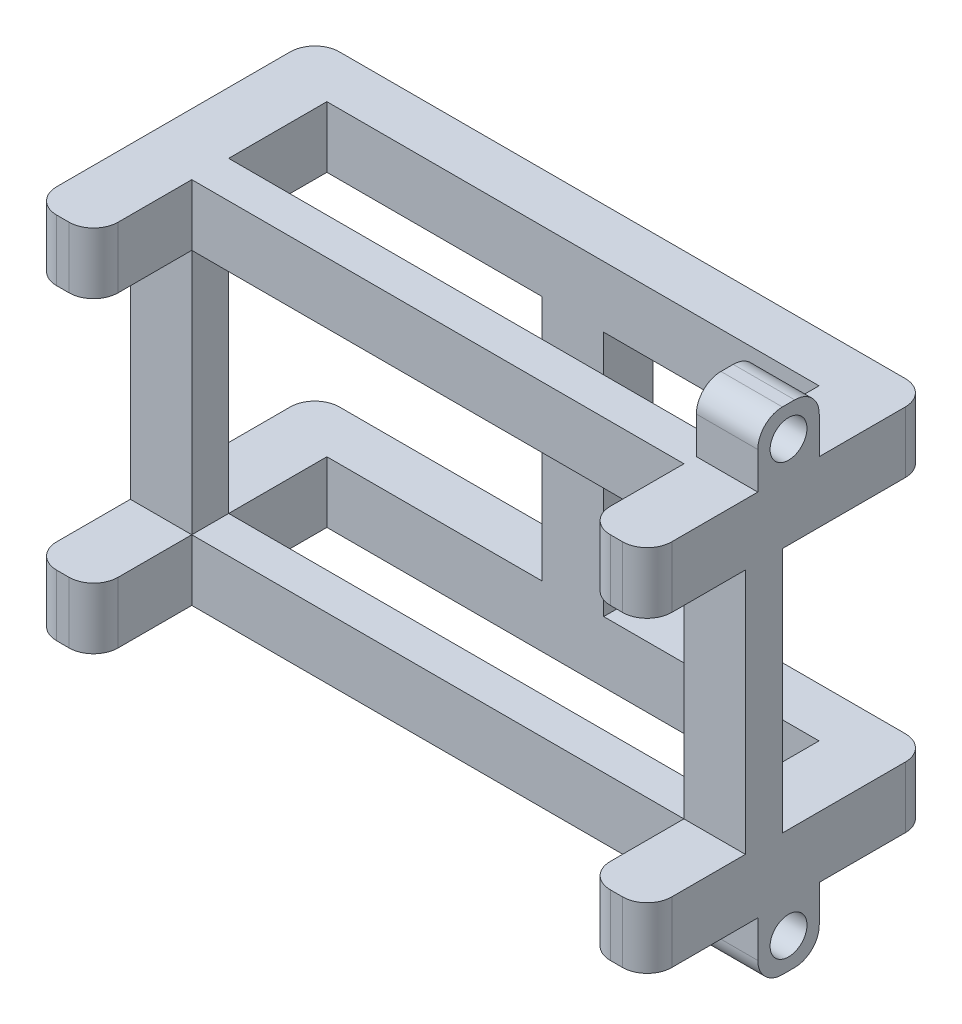
SolidWorks part; units mm, degrees
ref_plane "Front Plane" through (0, 0, 0) normal (0, 0, 1) x (1, 0, 0)
ref_plane "Top Plane" through (0, 0, 0) normal (0, 1, 0) x (1, 0, 0)
ref_plane "Right Plane" through (0, 0, 0) normal (1, 0, 0) x (0, 0, -1)
sketch "Sketch1" plane through (0, 0, 0) normal (0, 0, 1) x (1, 0, 0)
  line L0 (20.02, 5) -> (20.02, -25.04) construction
  line L1 (0, 0) -> (40.04, 0)
  line L2 (0, 0) -> (0, -20.04)
  line L3 (0, -20.04) -> (40.04, -20.04)
  line L4 (40.04, 0) -> (40.04, -20.04)
  line L5 (-5, 5) -> (45.04, 5)
  line L6 (-5, 5) -> (-5, -25.04)
  line L7 (-5, -25.04) -> (45.04, -25.04)
  line L8 (45.04, 5) -> (45.04, -25.04)
  line L10 (17.52, 0) -> (22.52, 0)
  line L11 (17.52, 0) -> (17.52, -20.04)
  line L12 (17.52, -20.04) -> (22.52, -20.04)
  line L13 (22.52, 0) -> (22.52, -20.04)
  line L14 (17.52, 0) -> (22.52, -20.04) construction
  line L15 (17.52, -20.04) -> (22.52, 0) construction
  point P11 (20.02, -10.02)
  dimension "D1" = 40.04
  dimension "D2" = 20.04
  dimension "D3" = 5
  dimension "D4" = 5
  dimension "D5" = 5
  dimension "D6" = 5
  dimension "D7" = 30.04
  dimension "D8" = 5
extrude "Boss-Extrude2" add sketch "Sketch1" along normal blind 28 contours L8 L5 L6 L7 L1 L4 L3 L2 | L13 L12 L11 L10
sketch "Sketch2" plane through (0, 0, 0) normal (0, 0, -1) x (-1, 0, 0)
  line L1 (-45.04, 5) -> (5, 5)
  line L2 (-45.04, 5) -> (-45.04, -25.04)
  line L3 (-45.04, -25.04) -> (5, -25.04)
  line L4 (5, 5) -> (5, -25.04)
  line L5 (-22.52, 0) -> (-40.04, 0)
  line L6 (-22.52, 0) -> (-22.52, -20.04)
  line L7 (-22.52, -20.04) -> (-40.04, -20.04)
  line L8 (-40.04, 0) -> (-40.04, -20.04)
  line L9 (-17.52, 0) -> (0, 0)
  line L10 (-17.52, 0) -> (-17.52, -20.04)
  line L11 (-17.52, -20.04) -> (0, -20.04)
  line L12 (0, 0) -> (0, -20.04)
extrude "Boss-Extrude3" add sketch "Sketch2" along normal blind 5
sketch "Sketch3" plane through (0, 0, 28) normal (0, 0, 1) x (1, 0, 0)
  line L6 (17.52, 0) -> (22.52, 0)
  line L7 (17.52, 0) -> (17.52, -20.04)
  line L8 (17.52, -20.04) -> (22.52, -20.04)
  line L9 (22.52, 0) -> (22.52, -20.04)
extrude "Cut-Extrude1" cut sketch "Sketch3" against normal blind 27
sketch "Sketch4" plane through (0, 0, -5) normal (0, 0, -1) x (-1, 0, 0)
  line L0 (-40.04, -20.04) -> (-45.04, -20.04) construction
  line L1 (-45.04, 5) -> (-45.04, -25.04) construction
  line L2 (-45.04, -20.04) -> (5, -20.04) construction
  line L3 (5, -25.04) -> (5, 5) construction
  line L4 (5, -20.04) -> (0, 0) construction
  line L5 (0, 0) -> (-45.04, 0) construction
  line L6 (-45.04, 0) -> (5, 0) construction
  line L8 (-45.04, 0) -> (-40.04, 0)
  line L9 (-45.04, 0) -> (-45.04, -20.04)
  line L10 (-45.04, -20.04) -> (-40.04, -20.04)
  line L11 (-40.04, 0) -> (-40.04, -20.04)
  line L12 (0, 0) -> (5, 0)
  line L13 (0, 0) -> (0, -20.04)
  line L14 (0, -20.04) -> (5, -20.04)
  line L15 (5, 0) -> (5, -20.04)
extrude "Cut-Extrude3" cut sketch "Sketch4" against normal blind 27
sketch "Sketch5" plane through (0, 5, 0) normal (0, 1, 0) x (1, 0, 0)
  line L0 (-5, -28) -> (45.04, -28) construction
  line L1 (0, -28) -> (40.04, -28)
  line L2 (0, -28) -> (0, 0.9809)
  line L3 (0, 0.9809) -> (40.04, 0.9809)
  line L4 (40.04, -28) -> (40.04, 0.9809)
  line L5 (-5, -28) -> (-5, 5) construction
  dimension "D1" = 5
  dimension "D2" = 40.04
extrude "Cut-Extrude4" cut sketch "Sketch5" against normal blind 47
sketch "Sketch6" plane through (0, 0, 0) normal (1, 0, 0) x (0, 0, -1)
  line L0 (5, -20.04) -> (-28, -20.04) construction
  line L1 (-28, 5) -> (-28, -25.04) construction
  line L2 (-28, -20.04) -> (-28, 0) construction
  line L3 (-28, 0) -> (5, 0) construction
  line L4 (-11.5, 0) -> (-11.5, -25.04) construction
  line L5 (-28, -25.04) -> (5, -25.04) construction
  line L6 (-11.5, -25.04) -> (-11.5, -20.04) construction
  line L7 (-11.5, -20.04) -> (-11.5, 0) construction
  line L8 (-11.5, 0) -> (-11.5, 5) construction
  line L9 (-28, 5) -> (5, 5) construction
  line L10 (-11.5, -20.04) -> (-11.5, -25.04) construction
  line L11 (-14, 5) -> (-9, 5)
  line L12 (-14, 5) -> (-14, 0)
  line L13 (-14, 0) -> (-9, 0)
  line L14 (-9, 5) -> (-9, 0)
  line L15 (-14, 5) -> (-9, 0) construction
  line L16 (-14, 0) -> (-9, 5) construction
  line L18 (-14, -20.04) -> (-9, -20.04)
  line L19 (-14, -20.04) -> (-14, -25.04)
  line L20 (-14, -25.04) -> (-9, -25.04)
  line L21 (-9, -20.04) -> (-9, -25.04)
  line L22 (-14, -20.04) -> (-9, -25.04) construction
  line L23 (-14, -25.04) -> (-9, -20.04) construction
  point P12 (-11.5, 2.5)
  point P21 (-11.5, -22.54)
  dimension "D1" = 5
  dimension "D2" = 5
extrude "Boss-Extrude4" add sketch "Sketch6" along normal blind 45
sketch "Sketch7" plane through (45.04, 0, 0) normal (1, 0, 0) x (0, 0, -1)
  line L0 (-28, 5) -> (5, 5) construction
  line L1 (5, -25.04) -> (-18, -25.04)
  line L2 (5, -25.04) -> (5, 5)
  line L3 (5, 5) -> (-18, 5)
  line L4 (-18, -25.04) -> (-18, 5)
  line L6 (-28, 5) -> (-18, 5)
  line L7 (-28, 5) -> (-28, -25.04)
  line L8 (-28, -25.04) -> (-18, -25.04)
  line L9 (-18, 5) -> (-18, -25.04)
  line M2 (5, -20.04) -> (-22, -20.04)
  line M3 (-22, -20.04) -> (-22, 0)
  line M4 (-22, 0) -> (5, 0)
  line M6 (5, 5) -> (-28, 5)
  line M7 (-28, 5) -> (-28, -25.04)
  line M8 (-28, -25.04) -> (5, -25.04)
  dimension "D1" = 23
extrude "Cut-Extrude5" cut sketch "Sketch7" against normal blind 66 contours L4 M8 M2 M3 M4 M6 M7
sketch "Sketch8" plane through (0, -25.04, 0) normal (0, -1, 0) x (1, 0, 0)
  line L0 (0, 18) -> (0, -0.9809) construction
  line L1 (0, -0.9809) -> (40.04, -0.9809) construction
  line L2 (40.04, -0.9809) -> (40.04, 6.5) construction
  line L3 (0, 8.5096) -> (-5, 8.5096) construction
  line L4 (-5, 18) -> (-5, -5) construction
  line L5 (-5, 8.5096) -> (40.04, 8.5096) construction
  line L6 (40.04, 8.5096) -> (45.04, 8.5096) construction
  line L7 (45.04, 18) -> (45.04, -5) construction
  line L9 (-5, 10.0096) -> (0, 10.0096)
  line L10 (-5, 10.0096) -> (-5, 7.0096)
  line L11 (-5, 7.0096) -> (0, 7.0096)
  line L12 (0, 10.0096) -> (0, 7.0096)
  line L13 (-5, 10.0096) -> (0, 7.0096) construction
  line L14 (-5, 7.0096) -> (0, 10.0096) construction
  line L19 (40.04, 10.0096) -> (45.04, 10.0096)
  line L20 (40.04, 10.0096) -> (40.04, 7.0096)
  line L21 (40.04, 7.0096) -> (45.04, 7.0096)
  line L22 (45.04, 10.0096) -> (45.04, 7.0096)
  line L23 (40.04, 10.0096) -> (45.04, 7.0096) construction
  line L24 (40.04, 7.0096) -> (45.04, 10.0096) construction
  point P7 (42.54, 8.5096)
  point P12 (-2.5, 8.5096)
  point P21 (42.54, 8.5096)
  dimension "D1" = 3
extrude "Boss-Extrude5" add sketch "Sketch8" against normal blind 29
sketch "Sketch9" plane through (0, -25.04, 0) normal (0, -1, 0) x (-1, 0, 0)
  line L1 (0, -14) -> (-40.04, -14)
  line L2 (0, -14) -> (0, -9)
  line L3 (0, -9) -> (-40.04, -9)
  line L4 (-40.04, -14) -> (-40.04, -9)
extrude "Cut-Extrude6" cut sketch "Sketch9" against normal blind 51
sketch "Sketch10" plane through (0, -25.04, 0) normal (0, -1, 0) x (1, 0, 0)
  line L1 (0, 10.0096) -> (40.04, 10.0096)
  line L2 (0, 10.0096) -> (0, 7.0096)
  line L3 (0, 7.0096) -> (40.04, 7.0096)
  line L4 (40.04, 10.0096) -> (40.04, 7.0096)
  dimension "D1" = 3
extrude "Boss-Extrude6" add sketch "Sketch10" against normal blind 5
sketch "Sketch12" plane through (0, 5, 0) normal (0, 1, 0) x (1, 0, 0)
  line L1 (0, -7.0096) -> (40.04, -7.0096)
  line L2 (0, -7.0096) -> (0, -10.0096)
  line L3 (0, -10.0096) -> (40.04, -10.0096)
  line L4 (40.04, -7.0096) -> (40.04, -10.0096)
extrude "Boss-Extrude7" add sketch "Sketch12" against normal blind 5
fillet "Fillet1" radius 2 12 edges at (40.04, 2.5, 18) (0, 2.5, 18) (-5, 2.5, 18) (40.04, -22.54, 18) (0, -22.54, 18) (-5, -22.54, 18) (45.04, -22.54, 18) (45.04, 2.5, 18) (45.04, 2.5, -5) (-5, -22.54, -5) (45.04, -22.54, -5) (-5, 2.5, -5)
sketch "Sketch13" plane through (45.04, 0, 0) normal (1, 0, 0) x (0, 0, -1)
  line L0 (5, -25.02) -> (5, -25.04)
  line L1 (-18, 5) -> (5, 5)
  line L2 (-18, 5) -> (-18, 4.98)
  line L3 (-18, -25.04) -> (5, -25.04)
  line L4 (5, 5) -> (5, 4.98)
  line L5 (-18, 4.98) -> (5, 4.98)
  line L7 (-18, -25.02) -> (5, -25.02)
  line L9 (-18, -25.02) -> (-18, -25.04)
  dimension "D1" = 0.02
  dimension "D2" = 0.02
extrude "Cut-Extrude7" cut sketch "Sketch13" against normal blind 87
sketch "Sketch14" plane through (45.04, 0, 0) normal (1, 0, 0) x (0, 0, -1)
  line L0 (-6.5, 4.98) -> (-6.5, 9.4794) construction
  line L1 (-18, 4.98) -> (5, 4.98)
  line L2 (-18, 4.98) -> (-18, -25.02)
  line L3 (-18, -25.02) -> (5, -25.02)
  line L4 (5, 4.98) -> (5, -25.02)
  line L5 (-6.5, 9.4794) -> (-6.5, -29.2806) construction
  line L7 (-9, 9.98) -> (-4, 9.98)
  line L8 (-9, 9.98) -> (-9, 4.98)
  line L9 (-9, 4.98) -> (-4, 4.98)
  line L10 (-4, 9.98) -> (-4, 4.98)
  line L11 (-9, 9.98) -> (-4, 4.98) construction
  line L12 (-9, 4.98) -> (-4, 9.98) construction
  line L13 (-9, -30.02) -> (-4, -30.02)
  line L14 (-9, -30.02) -> (-9, -25.02)
  line L15 (-9, -25.02) -> (-4, -25.02)
  line L16 (-4, -30.02) -> (-4, -25.02)
  line L17 (-9, -30.02) -> (-4, -25.02) construction
  line L18 (-9, -25.02) -> (-4, -30.02) construction
  circle A0 centre (-6.5, -27.52) radius 1.5
  circle A1 centre (-6.5, 7.48) radius 1.5
  point P8 (-6.5, 7.48)
  point P14 (-6.5, -27.52)
  dimension "D9" = 3
  dimension "D10" = 3
  dimension "D1" = 23
  dimension "D2" = 30
  dimension "D3" = 11.5
  dimension "D4" = 5
  dimension "D5" = 5
  dimension "D6" = 5
  dimension "D7" = 5
  dimension "D8" = 5
extrude "Boss-Extrude8" add sketch "Sketch14" against normal blind 5 contours L13 L16 L3 L14 A0 | L10 L7 L8 L1 A1
fillet "Fillet2" radius 2 4 edges at (42.54, 9.98, 9) (42.54, 9.98, 4) (42.54, -30.02, 4) (42.54, -30.02, 9)
